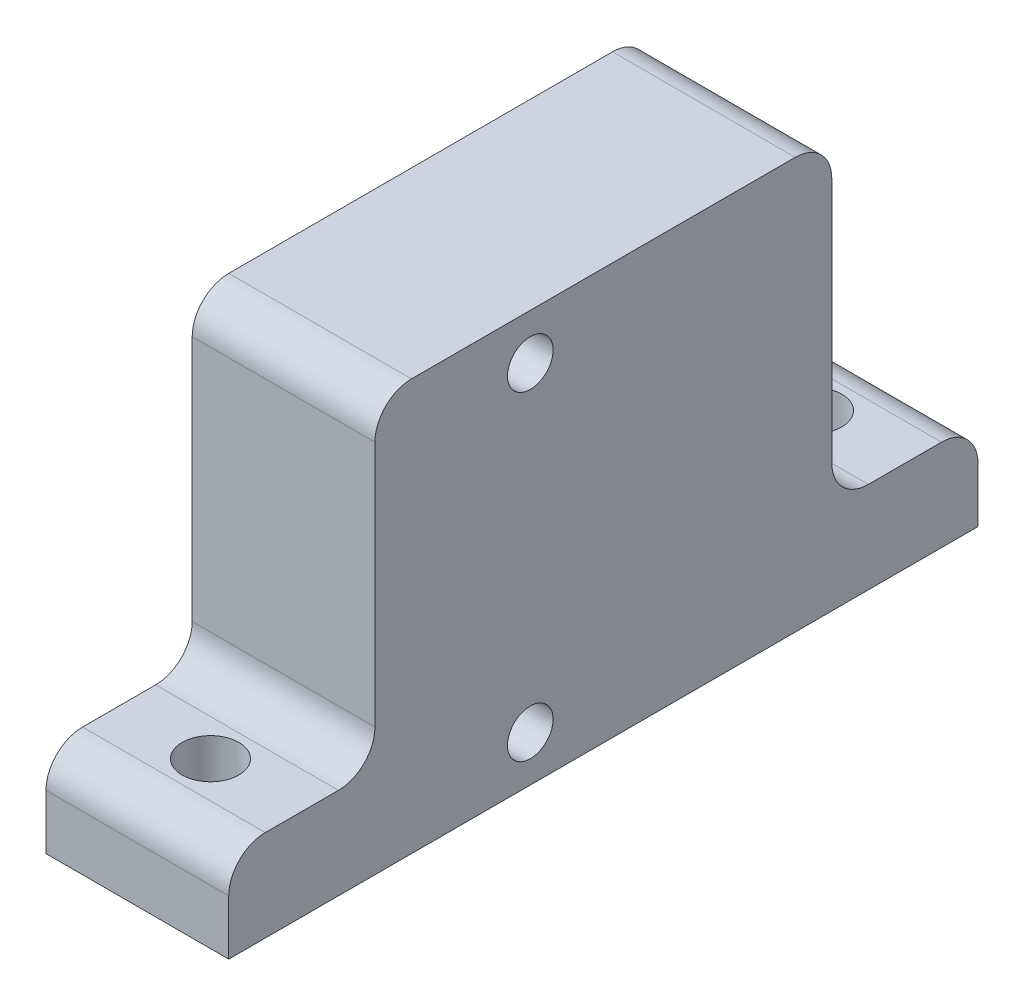
SolidWorks part; units mm, degrees
ref_plane "Front Plane" through (0, 0, 0) normal (0, 0, 1) x (1, 0, 0)
ref_plane "Top Plane" through (0, 0, 0) normal (0, 1, 0) x (1, 0, 0)
ref_plane "Right Plane" through (0, 0, 0) normal (1, 0, 0) x (0, 0, -1)
sketch "Sketch1" plane through (0, 0, 0) normal (1, 0, 0) x (0, 0, -1)
  line L0 (0, 8.75) -> (0, -8.75) construction
  line L1 (-8.5, 11.25) -> (16.5, 11.25)
  line L2 (-8.5, 11.25) -> (-8.5, -11.25)
  line L3 (-8.5, -11.25) -> (16.5, -11.25)
  line L4 (16.5, 11.25) -> (16.5, -11.25)
  line L5 (-8.5, 0) -> (16.5, 0) construction
  circle A0 centre (0, 8.75) radius 1.25
  circle A1 centre (0, -8.75) radius 1.25
  point P0 (0, 0)
  point P8 (0, 0)
  dimension "D3" = 2.5
  dimension "D1" = 22.5
  dimension "D2" = 17.5
  dimension "D4" = 8.5
  dimension "D5" = 25
extrude "Boss-Extrude1" add sketch "Sketch1" along normal blind 10
sketch "Sketch4" plane through (0, 0, -16.5) normal (0, 0, -1) x (-1, 0, 0)
  line L0 (0, -11.25) -> (0, 11.25) construction
  line L1 (-10, -11.25) -> (0, -11.25)
  line L2 (-10, -11.25) -> (-10, -6.25)
  line L3 (-10, -6.25) -> (0, -6.25)
  line L4 (0, -11.25) -> (0, -6.25)
  dimension "D1" = 5
extrude "Boss-Extrude3" add sketch "Sketch4" along normal blind 8
sketch "Sketch5" plane through (0, 0, 8.5) normal (0, 0, 1) x (1, 0, 0)
  line L0 (10, 11.25) -> (10, -11.25) construction
  line L1 (0, -11.25) -> (10, -11.25)
  line L2 (0, -11.25) -> (0, -6.25)
  line L3 (0, -6.25) -> (10, -6.25)
  line L4 (10, -11.25) -> (10, -6.25)
  dimension "D1" = 5
extrude "Boss-Extrude4" add sketch "Sketch5" along normal blind 8
fillet "Fillet1" radius 2 6 edges at (5, -6.25, 16.5) (5, -6.25, -24.5) (5, 11.25, -16.5) (5, 11.25, 8.5)
sketch "Sketch6" plane through (0, -6.25, 0) normal (0, 1, 0) x (1, 0, 0)
  line L0 (5, -14.5) -> (5, -10.5) construction
  line L1 (0, -14.5) -> (10, -14.5) construction
  line L2 (10, -10.5) -> (0, -10.5) construction
  circle A0 centre (5, -12.5) radius 1.55
  point P6 (5, -12.5)
  dimension "D1" = 3.1
extrude "Cut-Extrude1" cut sketch "Sketch6" against normal up to next
sketch "Sketch7" plane through (0, -6.25, 0) normal (0, 1, 0) x (1, 0, 0)
  line L0 (5, 18.5) -> (5, 22.5) construction
  line L1 (0, 18.5) -> (10, 18.5) construction
  line L2 (10, 22.5) -> (0, 22.5) construction
  circle A0 centre (5, 20.5) radius 1.55
  point P6 (5, 20.5)
  dimension "D1" = 3.1
extrude "Cut-Extrude2" cut sketch "Sketch7" against normal up to next
